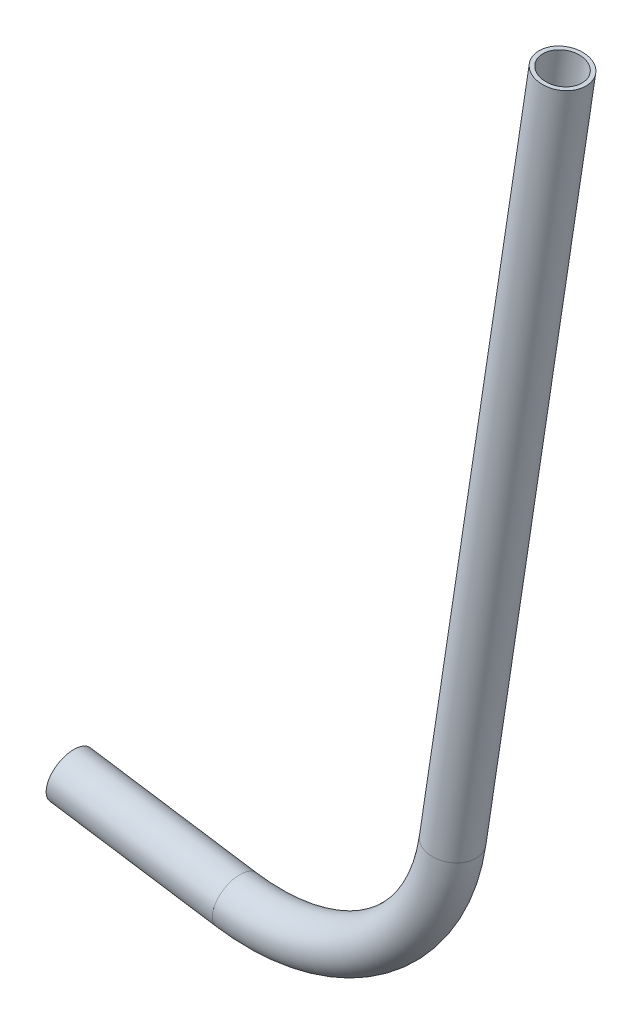
SolidWorks part; units mm, degrees
ref_plane "Front Plane" through (0, 0, 0) normal (0, 0, 1) x (1, 0, 0)
ref_plane "Top Plane" through (0, 0, 0) normal (0, 1, 0) x (1, 0, 0)
ref_plane "Right Plane" through (0, 0, 0) normal (1, 0, 0) x (0, 0, -1)
sketch "Sketch1" plane through (0, 0, 0) normal (0, 0, 1) x (1, 0, 0)
  line L0 (29.5904, 130.713) -> (74.0404, 123.9628)
  line L2 (131.8916, 166.56) -> (161.2894, 360.146)
  arc A0 (74.0404, 123.9628) -> (131.8916, 166.56) centre (81.6674, 174.187) ccw
  dimension "D1" = 50.8
  dimension "D2" = 44.45
other "Pipe 0.5 SCH 40(1)"
ref_plane "Plane1" through (29.5904, 130.713, 0) normal (0.9887, -0.1501, 0) x (0.1501, 0.9887, 0)
sketch "Sketch11" plane through (29.5904, 130.713, 0) normal (0.9887, -0.1501, 0) x (0.1501, 0.9887, 0)
  circle A0 centre (0, 0) radius 5.2832
  circle A1 centre (0, 0) radius 6.35
  point P5 (0, 0)
  dimension "In_dia" = 10.5664
  dimension "Out_dia" = 12.7
